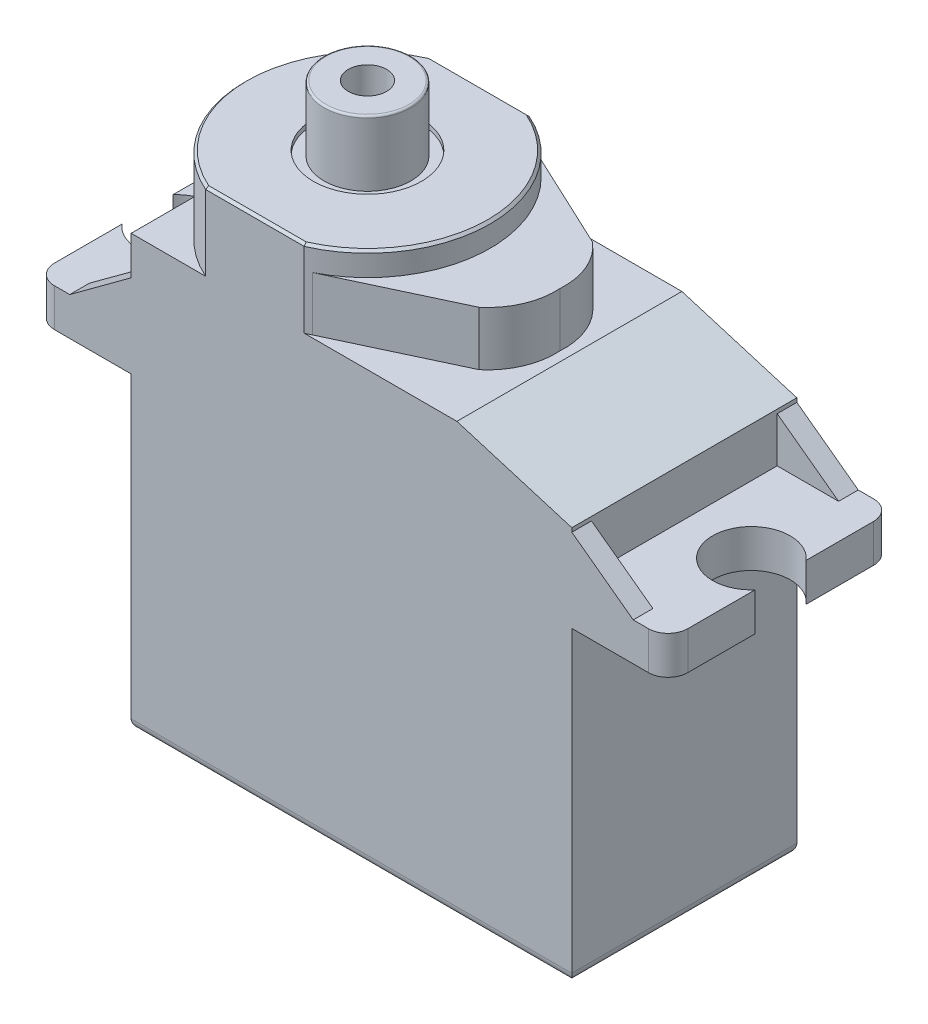
SolidWorks part; units mm, degrees
ref_plane "Front Plane" through (0, 0, 0) normal (0, 0, 1) x (1, 0, 0)
ref_plane "Top Plane" through (0, 0, 0) normal (0, 1, 0) x (1, 0, 0)
ref_plane "Right Plane" through (0, 0, 0) normal (1, 0, 0) x (0, 0, -1)
sketch "Sketch1" plane through (0, 0, 0) normal (0, 1, 0) x (1, 0, 0)
  line L1 (0, 0) -> (-22.7838, 0)
  line L2 (0, 0) -> (0, -11.6332)
  line L3 (0, -11.6332) -> (-22.7838, -11.6332)
  line L4 (-22.7838, 0) -> (-22.7838, -11.6332)
  dimension "D1" = 11.6332
  dimension "D2" = 22.7838
extrude "Boss-Extrude1" add sketch "Sketch1" along normal blind 15.9512
fillet "Fillet1" radius 0.508 4 edges at (-11.3919, 0, 0) (-22.7838, 0, 5.8166) (-11.3919, 0, 11.6332) (0, 0, 5.8166)
sketch "Sketch5" plane through (0, 0, 11.6332) normal (0, 0, 1) x (1, 0, 0)
  line L0 (4.9784, 15.9512) -> (-27.7622, 15.9512)
  line L1 (-27.7622, 15.9512) -> (-27.7622, 17.9197)
  line L2 (-27.7622, 17.9197) -> (-22.7838, 17.9197)
  line L3 (-22.7838, 17.9197) -> (-22.7838, 26.2636)
  line L4 (-22.7838, 26.2636) -> (-7.5127, 26.2636)
  line L5 (-7.5127, 26.2636) -> (-7.5127, 22.2504)
  line L6 (-7.5127, 22.2504) -> (-5.9436, 22.2504)
  line L7 (-5.9436, 22.2504) -> (0, 20.4597)
  line L8 (0, 20.4597) -> (0, 17.9197)
  line L9 (0, 17.9197) -> (4.9784, 17.9197)
  line L10 (4.9784, 17.9197) -> (4.9784, 15.9512)
  line L11 (4.9784, 15.9512) -> (4.9923, 15.8841)
  line L12 (0, 15.9512) -> (0, 0.508) construction
  line L13 (-22.7838, 15.9512) -> (-22.7838, 0.508) construction
  line L14 (-0.508, 0) -> (-22.2758, 0) construction
  line M4 (0, 15.9512) -> (-22.7838, 15.9512)
  dimension "D1" = 4.9784
  dimension "D2" = 4.9784
  dimension "D3" = 1.9685
  dimension "D4" = 26.2636
  dimension "D5" = 5.9436
  dimension "D6" = 2.54
  dimension "D7" = 22.2504
  dimension "D8" = 1.5691
extrude "Boss-Extrude3" add sketch "Sketch5" against normal up to surface (11.6332 mm away) contours L10 L9 L8 L7 L6 L5 L4 L3 L2 L1 L0 M4 up to face at (-11.3919, 8.2296, 0)
sketch "Sketch6" plane through (0, 26.2636, 0) normal (0, 1, 0) x (1, 0, 0)
  line L0 (-16.383, 0) -> (-16.383, -11.6332) construction
  line L1 (-22.7838, 0) -> (-7.5127, 0)
  line L2 (-22.7838, 0) -> (-22.7838, -11.6332)
  line L3 (-22.7838, -11.6332) -> (-7.5127, -11.6332)
  line L4 (-7.5127, 0) -> (-7.5127, -11.6332)
  line L6 (0, 0) -> (0, -11.6332) construction
  circle A0 centre (-16.383, -5.8166) radius 6.35
  line M1 (-7.5127, -11.6332) -> (-7.5127, 0)
  line M2 (-7.5127, 0) -> (-22.7838, 0)
  line M3 (-22.7838, 0) -> (-22.7838, -11.6332)
  line M4 (-22.7838, -11.6332) -> (-7.5127, -11.6332)
  dimension "D1" = 12.7
  dimension "D2" = 16.383
extrude "Cut-Extrude1" cut sketch "Sketch6" against normal up to surface (4.0132 mm away) contours A0 M2 M3 M4 | A0 M4 M1 M2 up to face at (-6.7282, 22.2504, 5.8166)
chamfer "Chamfer1" distance 0.127 angle 45 4 edges at (-16.383, 26.2636, 0) (-16.383, 26.2636, 11.6332) (-10.033, 26.2636, 5.8166) (-22.733, 26.2636, 5.8166)
fillet "Fillet2" radius 1.016 4 edges at (-27.7622, 16.9354, 0) (-27.7622, 16.9354, 11.6332) (4.9784, 16.9354, 0) (4.9784, 16.9354, 11.6332)
sketch "Sketch7" plane through (0, 17.9197, 0) normal (0, 1, 0) x (1, 0, 0)
  line L0 (3.4671, 0) -> (3.4671, -11.6332) construction
  line L1 (3.9624, 0) -> (0, 0) construction
  line L2 (0, -11.6332) -> (3.9624, -11.6332) construction
  line L3 (-26.2509, -11.6332) -> (-26.2509, 0) construction
  line L4 (-26.7462, -11.6332) -> (-22.7838, -11.6332) construction
  line L5 (-22.7838, 0) -> (-26.7462, 0) construction
  line L6 (3.4671, -5.8166) -> (4.9784, -5.8166) construction
  line L7 (4.9784, -1.016) -> (4.9784, -10.6172) construction
  line L8 (-26.2509, -5.8166) -> (-27.7622, -5.8166) construction
  line L9 (-27.7622, -1.016) -> (-27.7622, -10.6172) construction
  circle A0 centre (3.4671, -5.8166) radius 2.0066
  circle A1 centre (-26.2509, -5.8166) radius 2.0066
  dimension "D1" = 4.0132
  dimension "D2" = 29.718
extrude "Cut-Extrude2" cut sketch "Sketch7" against normal through all
sketch "Sketch8" plane through (0, 22.2504, 0) normal (0, 1, 0) x (1, 0, 0)
  line L0 (-5.9436, -5.8166) -> (-10.033, -5.8166) construction
  line L1 (-5.9436, 0) -> (-5.9436, -11.6332) construction
  line L2 (-13.8355, 0) -> (-7.6791, -2.888)
  line L3 (-13.8355, -11.6332) -> (-7.6791, -8.7452)
  arc A0 (-13.8355, -11.6332) -> (-13.8355, 0) centre (-16.383, -5.8166) ccw construction
  arc A1 (-7.6791, -2.888) -> (-6.4334, -5.8166) centre (-9.9323, -5.5757) cw
  arc A2 (-7.6791, -8.7452) -> (-6.4334, -5.8166) centre (-9.9323, -6.0575) ccw
  arc M3 (-13.8355, 0) -> (-13.8355, -11.6332) centre (-16.383, -5.8166) cw
extrude "Boss-Extrude4" add sketch "Sketch8" along normal blind 2.794 contours A2 L0 L3 M3 | L0 A1 L2 M3
sketch "Sketch9" plane through (0, 26.2636, 0) normal (0, 1, 0) x (1, 0, 0)
  circle A0 centre (-16.383, -5.8166) radius 2.794
  dimension "D1" = 5.588
extrude "Cut-Extrude3" cut sketch "Sketch9" against normal blind 0.254
sketch "Sketch10" plane through (0, 0, 11.6332) normal (0, 0, 1) x (1, 0, 0)
  line L0 (0, 20.2565) -> (3.175, 17.9197)
  line L1 (0, 17.9197) -> (3.9624, 17.9197) construction
  line L2 (3.175, 17.9197) -> (0, 17.9197)
  line L3 (0, 17.9197) -> (0, 20.2565)
  line L4 (-22.7838, 17.9197) -> (-22.7838, 20.2565)
  line L5 (-22.7838, 17.9197) -> (-22.7838, 22.2504) construction
  line L6 (-22.7838, 20.2565) -> (-25.9588, 17.9197)
  line L7 (-26.7462, 17.9197) -> (-22.7838, 17.9197) construction
  line L8 (-25.9588, 17.9197) -> (-22.7838, 17.9197)
  line L9 (0, 20.4597) -> (0, 17.9197) construction
  dimension "D1" = 3.175
  dimension "D2" = 2.3368
extrude "Boss-Extrude5" add sketch "Sketch10" against normal blind 1.016
sketch "Sketch11" plane through (0, 0, 0) normal (0, 0, -1) x (-1, 0, 0)
  line L3 (22.7838, 20.2565) -> (22.7838, 17.9197)
  line L4 (25.9588, 17.9197) -> (22.7838, 20.2565)
  line L5 (22.7838, 17.9197) -> (25.9588, 17.9197)
  line L6 (22.7838, 20.2565) -> (22.7838, 17.9197)
  line L7 (25.9588, 17.9197) -> (22.7838, 20.2565)
  line L8 (22.7838, 17.9197) -> (25.9588, 17.9197)
  line L9 (0, 20.2565) -> (-3.175, 17.9197)
  line L10 (-3.175, 17.9197) -> (0, 17.9197)
  line L11 (0, 17.9197) -> (0, 20.2565)
  line L12 (0, 20.2565) -> (-3.175, 17.9197)
  line L13 (-3.175, 17.9197) -> (0, 17.9197)
  line L14 (0, 17.9197) -> (0, 20.2565)
  dimension "D1" = 0
  dimension "D2" = 0
extrude "Boss-Extrude6" add sketch "Sketch11" against normal blind 1.016
sketch "Sketch12" plane through (0, 26.0096, 0) normal (0, 1, 0) x (1, 0, 0)
  circle A0 centre (-16.383, -5.8166) radius 2.2479
  circle A1 centre (-16.383, -5.8166) radius 0.9906
  dimension "D1" = 4.4958
  dimension "D2" = 1.9812
extrude "Boss-Extrude10" add sketch "Sketch12" along direction (0, -1, 0) on the side of the normal blind 3.3782 contours A0 A1
fillet "Fillet3" radius 0.1016 1 edges at (-16.383, 29.3878, 8.0645)
